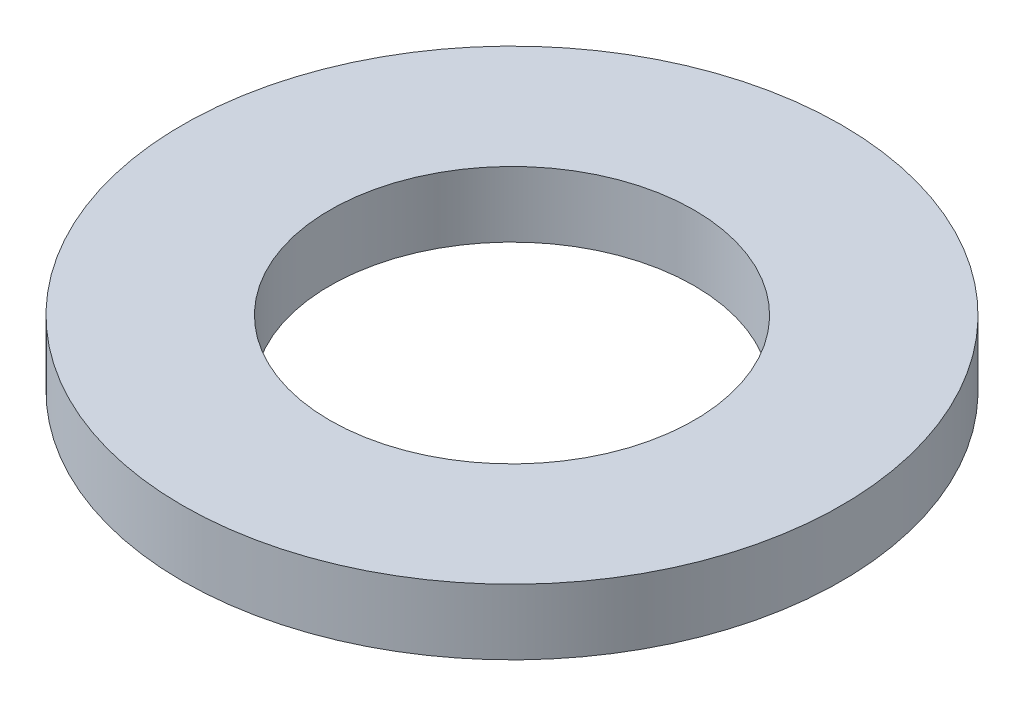
SolidWorks part; units mm, degrees
ref_plane "Front Plane" through (0, 0, 0) normal (0, 0, 1) x (1, 0, 0)
ref_plane "Top Plane" through (0, 0, 0) normal (0, 1, 0) x (1, 0, 0)
ref_plane "Right Plane" through (0, 0, 0) normal (1, 0, 0) x (0, 0, -1)
sketch "Sketch1" plane through (0, 0, 0) normal (0, 1, 0) x (1, 0, 0)
  circle A0 centre (0, 0) radius 18.6563
  dimension "OD" = 37.3126
extrude "Boss-Extrude1" add sketch "Sketch1" along normal blind 3.7084
sketch "Sketch5" plane through (0, 3.7084, 0) normal (0, 1, 0) x (-1, 0, 0)
  circle A0 centre (0, 0) radius 10.3124
  dimension "ID" = 20.6248
extrude "Cut-Extrude1" cut sketch "Sketch5" against normal through all
